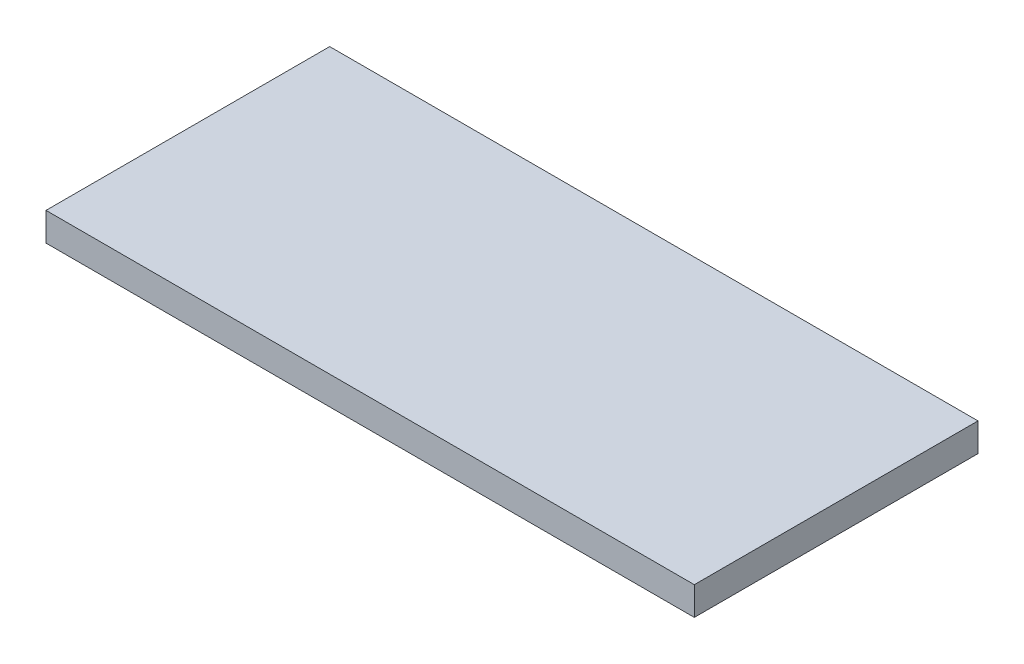
SolidWorks part; units mm, degrees
ref_plane "Front Plane" through (0, 0, 0) normal (0, 0, 1) x (1, 0, 0)
ref_plane "Top Plane" through (0, 0, 0) normal (0, 1, 0) x (1, 0, 0)
ref_plane "Right Plane" through (0, 0, 0) normal (1, 0, 0) x (0, 0, -1)
sketch "Sketch1" plane through (0, 0, 0) normal (0, 1, 0) x (1, 0, 0)
  line L0 (-114.265, 50) -> (114.265, -50) construction
  line L1 (-114.265, 50) -> (114.265, 50)
  line L2 (-114.265, 50) -> (-114.265, -50)
  line L3 (-114.265, -50) -> (114.265, -50)
  line L4 (114.265, 50) -> (114.265, -50)
  dimension "D1" = 228.53
  dimension "D2" = 100
extrude "Boss-Extrude1" add sketch "Sketch1" along normal blind 10
